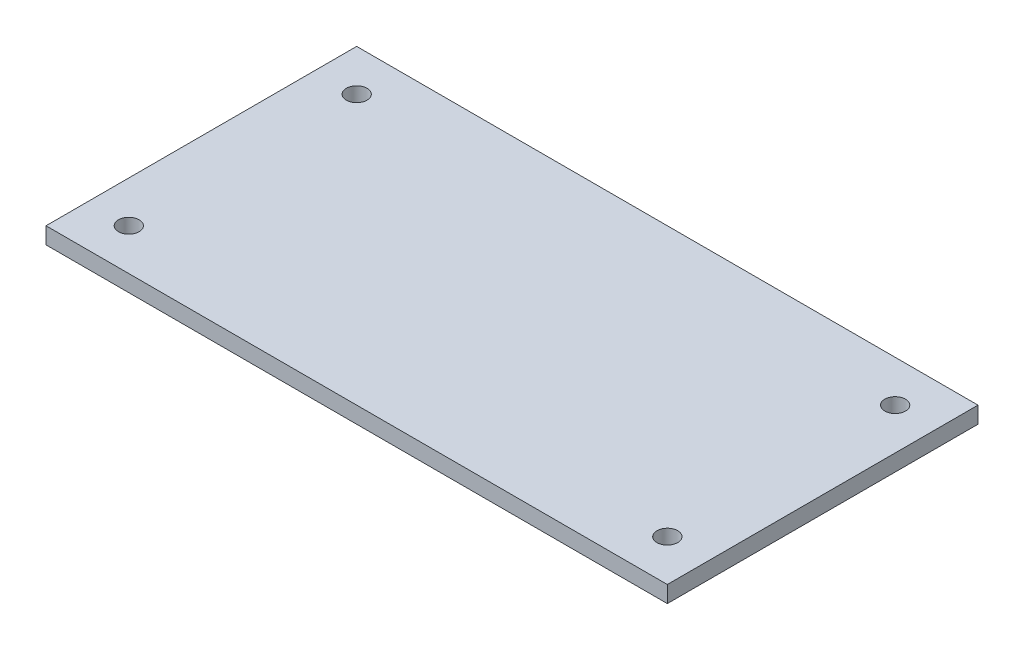
SolidWorks part; units mm, degrees
ref_plane "Front Plane" through (0, 0, 0) normal (0, 0, 1) x (1, 0, 0)
ref_plane "Top Plane" through (0, 0, 0) normal (0, 1, 0) x (1, 0, 0)
ref_plane "Right Plane" through (0, 0, 0) normal (1, 0, 0) x (0, 0, -1)
sketch "Sketch1" plane through (0, 0, 0) normal (0, 1, 0) x (1, 0, 0)
  line L0 (0, 37.5) -> (0, -37.5) construction
  line L1 (-75, -37.5) -> (75, -37.5)
  line L2 (-75, -37.5) -> (-75, 37.5)
  line L3 (-75, 37.5) -> (75, 37.5)
  line L4 (75, -37.5) -> (75, 37.5)
  line L5 (-75, -37.5) -> (75, 37.5) construction
  line L6 (-75, 37.5) -> (75, -37.5) construction
  line L7 (-75, 0) -> (75, 0) construction
  line L8 (-65, 37.5) -> (-65, -37.5) construction
  line L9 (65, 37.5) -> (65, -37.5) construction
  line L10 (-65, 8) -> (0, 8) construction
  circle A0 centre (-65, -27.5) radius 2.5
  circle A1 centre (-65, 27.5) radius 2.5
  circle A2 centre (65, -27.5) radius 2.5
  circle A3 centre (65, 27.5) radius 2.5
  point P0 (0, 0)
  dimension "D3" = 5
  dimension "D1" = 150
  dimension "D2" = 75
  dimension "D4" = 10
  dimension "D5" = 10
  dimension "D7" = 8
extrude "Boss-Extrude1" add sketch "Sketch1" along normal blind 4
